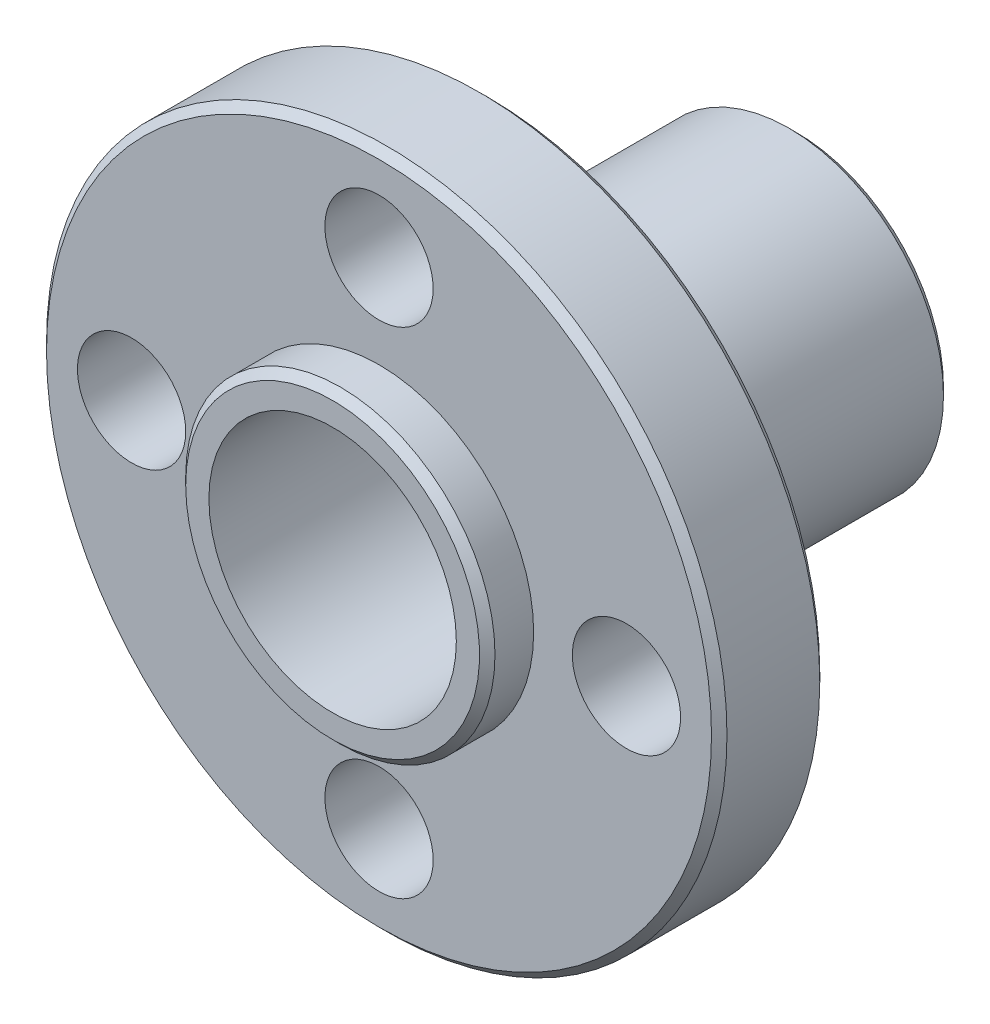
SolidWorks part; units mm, degrees
material "Brass"
ref_plane "Front Plane" through (0, 0, 0) normal (0, 0, 1) x (1, 0, 0)
ref_plane "Top Plane" through (0, 0, 0) normal (0, 1, 0) x (1, 0, 0)
ref_plane "Right Plane" through (0, 0, 0) normal (1, 0, 0) x (0, 0, -1)
sketch "Sketch1" plane through (0, 0, 0) normal (1, 0, 0) x (0, 0, -1)
  line L0 (0, 4) -> (15, 4)
  line L1 (15, 4) -> (15, 5)
  line L2 (15, 5) -> (5, 5)
  line L3 (5, 5) -> (5, 11)
  line L4 (5, 11) -> (1.5, 11)
  line L5 (1.5, 11) -> (1.5, 5)
  line L6 (1.5, 5) -> (0, 5)
  line L7 (0, 5) -> (0, 4)
  line L8 (-903.9733, 0) -> (44294.6902, 0) construction
  dimension "D1" = 8
  dimension "D2" = 10
  dimension "D3" = 1.5
  dimension "D4" = 3.5
  dimension "D5" = 10
  dimension "D6" = 22
revolve "Revolve1" add sketch "Sketch1" angle 360 about L8
chamfer "Chamfer1" distance 0.25 angle 45 4 edges at (5, 0, 0) (11, 0, -1.5) (11, 0, -5) (5, 0, -15)
sketch "Sketch2" plane through (0, 0, -1.5) normal (0, 0, 1) x (1, 0, 0)
  circle A0 centre (0, 0) radius 8 construction
  circle A1 centre (0, 8) radius 1.75
  circle A2 centre (8, 0) radius 1.75
  circle A3 centre (0, -8) radius 1.75
  circle A4 centre (-8, 0) radius 1.75
  dimension "D1" = 3.5
  dimension "D2" = 16
extrude "Cut-Extrude1" cut sketch "Sketch2" against normal up to next
